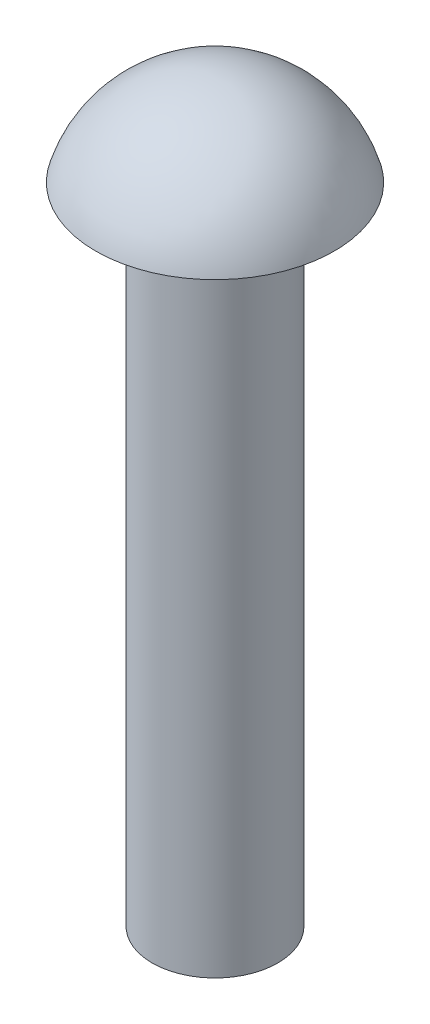
SolidWorks part; units mm, degrees
material "1060 Alloy"
ref_plane "Front Plane" through (0, 0, 0) normal (0, 0, 1) x (1, 0, 0)
ref_plane "Top Plane" through (0, 0, 0) normal (0, 1, 0) x (1, 0, 0)
ref_plane "Right Plane" through (0, 0, 0) normal (1, 0, 0) x (0, 0, -1)
sketch "Sketch1" plane through (0, 0, 0) normal (1, 0, 0) x (0, 0, -1)
  line L0 (0, 0) -> (0, -11.4) construction
  line L1 (0, -11.4) -> (0.975, -11.4)
  line L2 (0.975, -11.4) -> (0.975, -1.4)
  line L3 (0.975, -1.4) -> (1.85, -1.4)
  line L6 (0, 0) -> (0, -11.4)
  arc A0 (1.85, -1.4) -> (0, 0) centre (0, -1.9223) ccw
  dimension "D4" = 1.85
  dimension "D1" = 1.95
  dimension "D2" = 10
  dimension "D3" = 1.4
revolve "Revolve2" add sketch "Sketch1" angle 360 about L0
